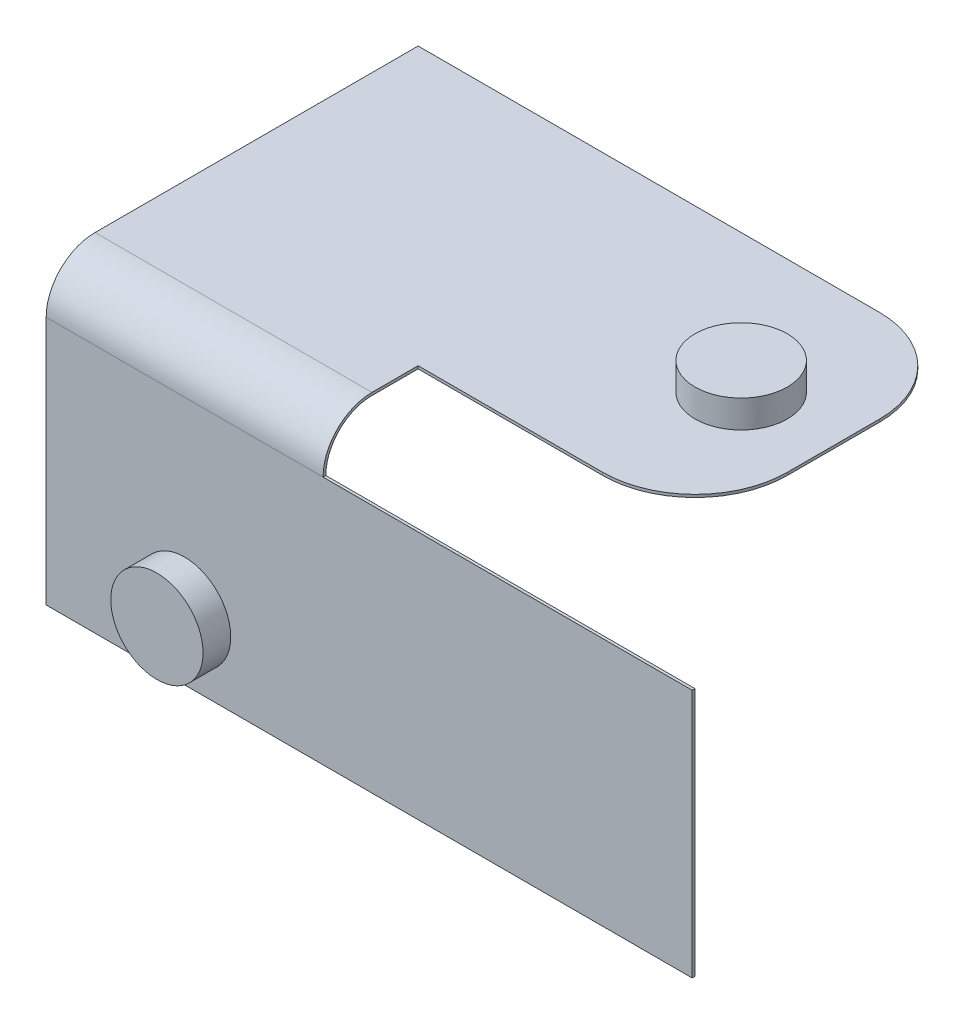
SolidWorks part; units mm, degrees
ref_plane "Front Plane" through (0, 0, 0) normal (0, 0, 1) x (1, 0, 0)
ref_plane "Top Plane" through (0, 0, 0) normal (0, 1, 0) x (1, 0, 0)
ref_plane "Right Plane" through (0, 0, 0) normal (1, 0, 0) x (0, 0, -1)
sketch "Sketch1" plane through (0, 0, 0) normal (0, 1, 0) x (1, 0, 0)
  line L1 (-3.6063, 1.1547) -> (-63.6063, 1.1547)
  line L2 (-3.6063, 1.1547) -> (-3.6063, -28.8453)
  line L3 (-3.6063, -28.8453) -> (-63.6063, -28.8453)
  line L4 (-63.6063, 1.1547) -> (-63.6063, -28.8453)
  dimension "D1" = 30
  dimension "D2" = 60
extrude "Boss-Extrude1" add sketch "Sketch1" along normal blind 0.3
ref_plane "Plane1" through (-63.6063, 0, 0) normal (-1, 0, 0) x (0, 0, 1)
sketch "Sketch6" plane through (-63.6063, 0, 0) normal (-1, 0, 0) x (0, 0, 1)
  line L0 (28.8453, 0.3) -> (33.8453, 0.3)
  line L1 (28.8453, 0) -> (33.8453, 0)
  line L2 (39.1453, -5) -> (39.1453, -32)
  line L3 (39.1453, -32) -> (38.8453, -32)
  line L4 (38.8453, -32) -> (38.8453, -5)
  line L5 (28.8453, 0) -> (28.8453, 0.3)
  arc A0 (33.8453, 0) -> (38.8453, -5) centre (33.8453, -5) cw
  arc A1 (33.8453, 0.3) -> (39.1453, -5) centre (33.8453, -5) cw
  dimension "D3" = 5.3
  dimension "D4" = 5
  dimension "D1" = 5
  dimension "D2" = 5
  dimension "D5" = 27
  dimension "D6" = 27
extrude "Boss-Extrude3" add sketch "Sketch6" against normal blind 30
sketch "Sketch7" plane through (0, 0, 39.1453) normal (0, 0, 1) x (1, 0, 0)
  line L0 (-33.6063, -32) -> (-63.6063, -32) construction
  line L1 (-63.6063, -32) -> (-63.6063, -5) construction
  circle A0 centre (-48.6063, -25) radius 5
  dimension "D3" = 10
  dimension "D1" = 7
  dimension "D2" = 15
extrude "Boss-Extrude4" add sketch "Sketch7" along normal blind 3 contours A0
sketch "Sketch8" plane through (0, 0.3, 0) normal (0, 1, 0) x (1, 0, 0)
  line L0 (-3.6063, 1.1547) -> (-63.6063, 1.1547) construction
  line L1 (-63.6063, 4.3532) -> (-63.6063, -4.3532) construction
  circle A0 centre (-13.6063, -13.8453) radius 5
  dimension "D1" = 15
  dimension "D3" = 10
  dimension "D2" = 50
extrude "Boss-Extrude5" add sketch "Sketch8" along normal blind 3
sketch "Sketch9" plane through (-33.6063, 0, 0) normal (1, 0, 0) x (0, 0, -1)
  line L1 (-39.1453, -5) -> (-38.8453, -5)
  line L2 (-39.1453, -5) -> (-39.1453, -32)
  line L3 (-39.1453, -32) -> (-38.8453, -32)
  line L4 (-38.8453, -5) -> (-38.8453, -32)
extrude "Boss-Extrude6" add sketch "Sketch9" along normal blind 40
fillet "Fillet1" radius 10 2 edges at (-3.6063, 0.15, -1.1547) (-3.6063, 0.15, 28.8453)
